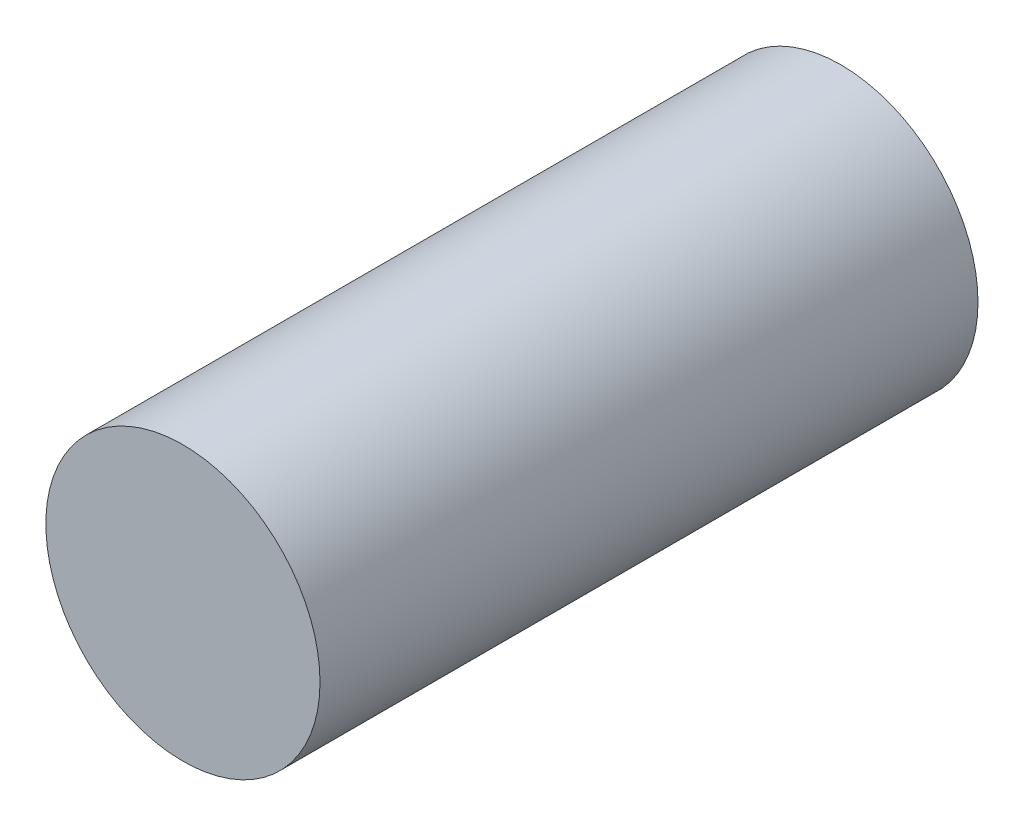
SolidWorks part; units mm, degrees
ref_plane "Front Plane" through (0, 0, 0) normal (0, 0, 1) x (1, 0, 0)
ref_plane "Top Plane" through (0, 0, 0) normal (0, 1, 0) x (1, 0, 0)
ref_plane "Right Plane" through (0, 0, 0) normal (1, 0, 0) x (0, 0, -1)
sketch "Sketch1" plane through (0, 0, -6) normal (0, 0, 1) x (1, 0, 0)
  circle A0 centre (28, 7.3) radius 3.75
  dimension "D1" = 7.5
extrude "Boss-Extrude1" add sketch "Sketch1" along normal blind 17 and the other way up to surface (1 mm away)
